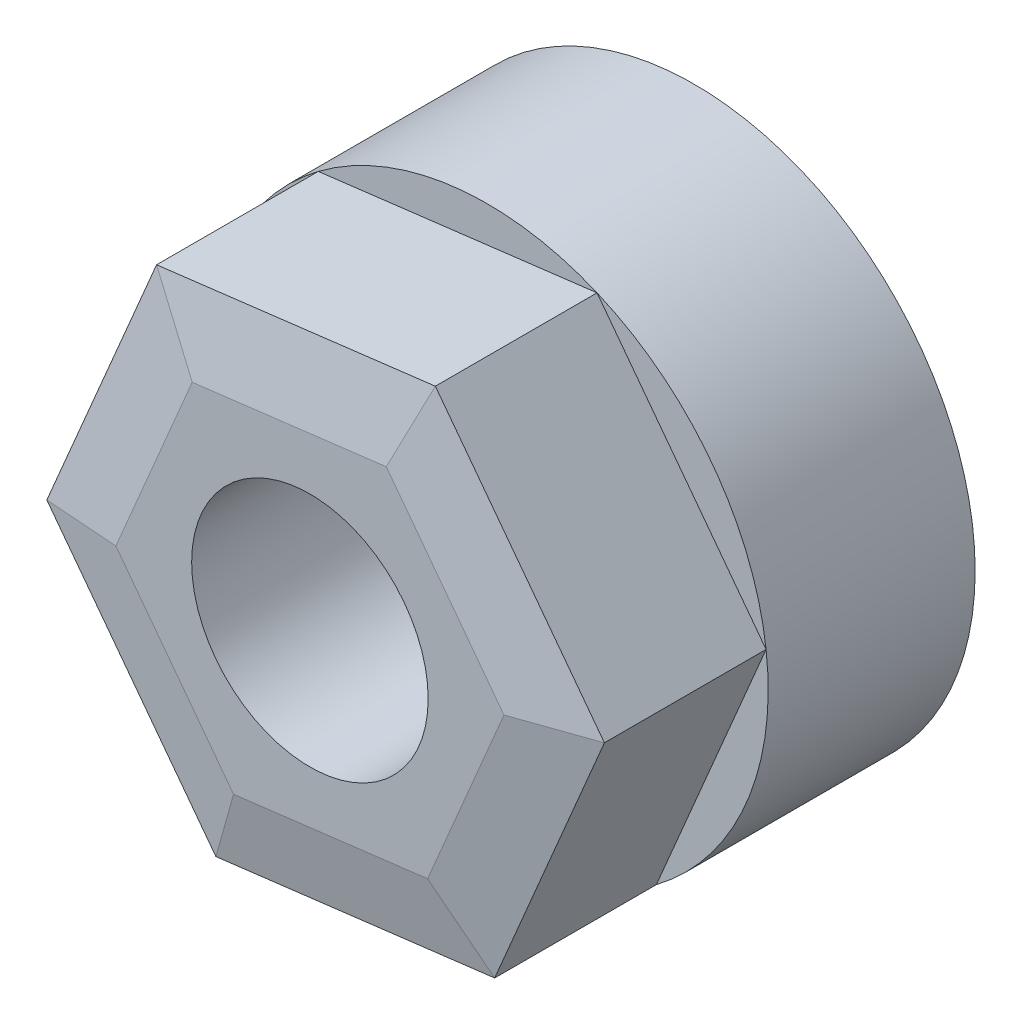
SolidWorks part; units mm, degrees
ref_plane "Alzado" through (0, 0, 0) normal (0, 0, 1) x (1, 0, 0)
ref_plane "Planta" through (0, 0, 0) normal (0, 1, 0) x (1, 0, 0)
ref_plane "Vista lateral" through (0, 0, 0) normal (1, 0, 0) x (0, 0, -1)
sketch "Croquis1" plane through (0, 0, 0) normal (0, 0, 1) x (1, 0, 0)
  circle A0 centre (0, 0) radius 9.5
  dimension "D1" = 19
extrude "Saliente-Extruir1" add sketch "Croquis1" along normal blind 7
sketch "Croquis2" plane through (0, 0, 7) normal (0, 0, 1) x (1, 0, 0)
  line L1 (3.7115, 8.745) -> (-5.7176, 7.5867)
  line L2 (-5.7176, 7.5867) -> (-9.4291, -1.1582)
  line L3 (-9.4291, -1.1582) -> (-3.7115, -8.745)
  line L4 (-3.7115, -8.745) -> (5.7176, -7.5867)
  line L5 (5.7176, -7.5867) -> (9.4291, 1.1582)
  line L6 (9.4291, 1.1582) -> (3.7115, 8.745)
  circle A0 centre (0, 0) radius 8.2272 construction
extrude "Saliente-Extruir2" add sketch "Croquis2" along normal blind 6
sketch "Croquis3" plane through (0, 0, 13) normal (0, 0, 1) x (1, 0, 0)
  circle A0 centre (0, 0) radius 4
  dimension "D1" = 8
extrude "Cortar-Extruir1" cut sketch "Croquis3" against normal through all
chamfer "Chaflán1" distance 2.5 angle 12 6 edges at (-7.5734, 3.2143, 13) (-1.0031, 8.1659, 13) (6.5703, 4.9516, 13) (7.5734, -3.2143, 13) (1.0031, -8.1659, 13) (-6.5703, -4.9516, 13)
